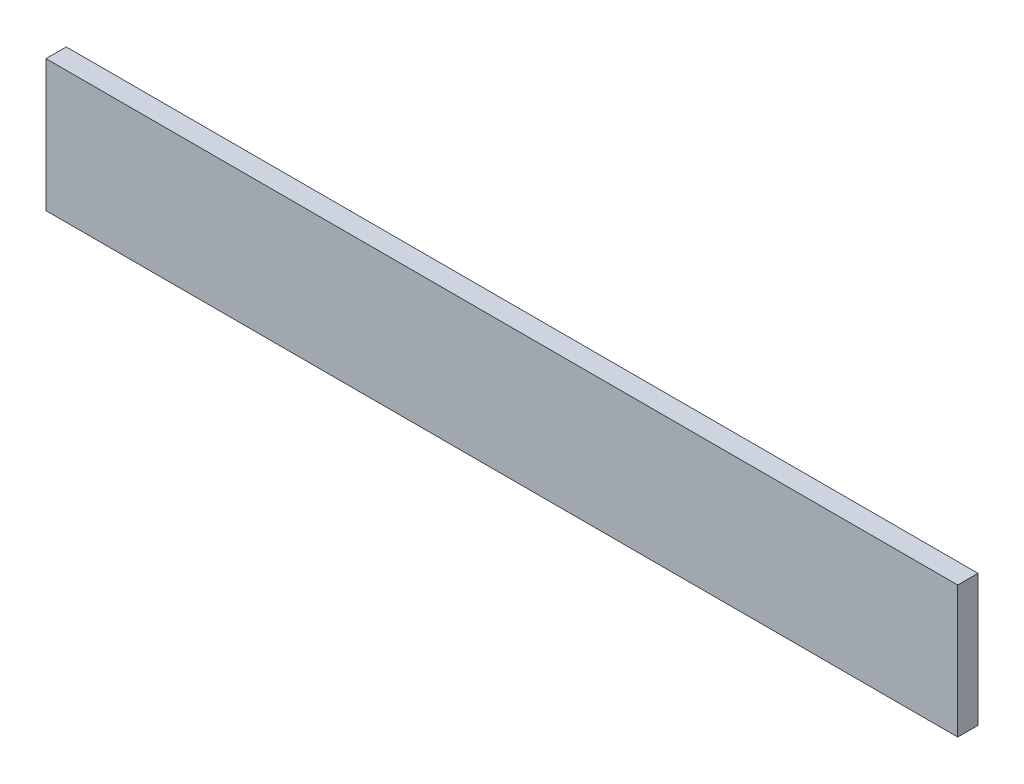
SolidWorks part; units mm, degrees
ref_plane "Front Plane" through (0, 0, 0) normal (0, 0, 1) x (1, 0, 0)
ref_plane "Top Plane" through (0, 0, 0) normal (0, 1, 0) x (1, 0, 0)
ref_plane "Right Plane" through (0, 0, 0) normal (1, 0, 0) x (0, 0, -1)
sketch "Sketch1" plane through (0, 0, 0) normal (0, 0, 1) x (1, 0, 0)
  line L1 (0, 0) -> (450, 0)
  line L2 (0, 0) -> (0, 65)
  line L3 (0, 65) -> (450, 65)
  line L4 (450, 0) -> (450, 65)
  dimension "D1" = 65
  dimension "D2" = 450
extrude "Boss-Extrude1" add sketch "Sketch1" along normal blind 10
